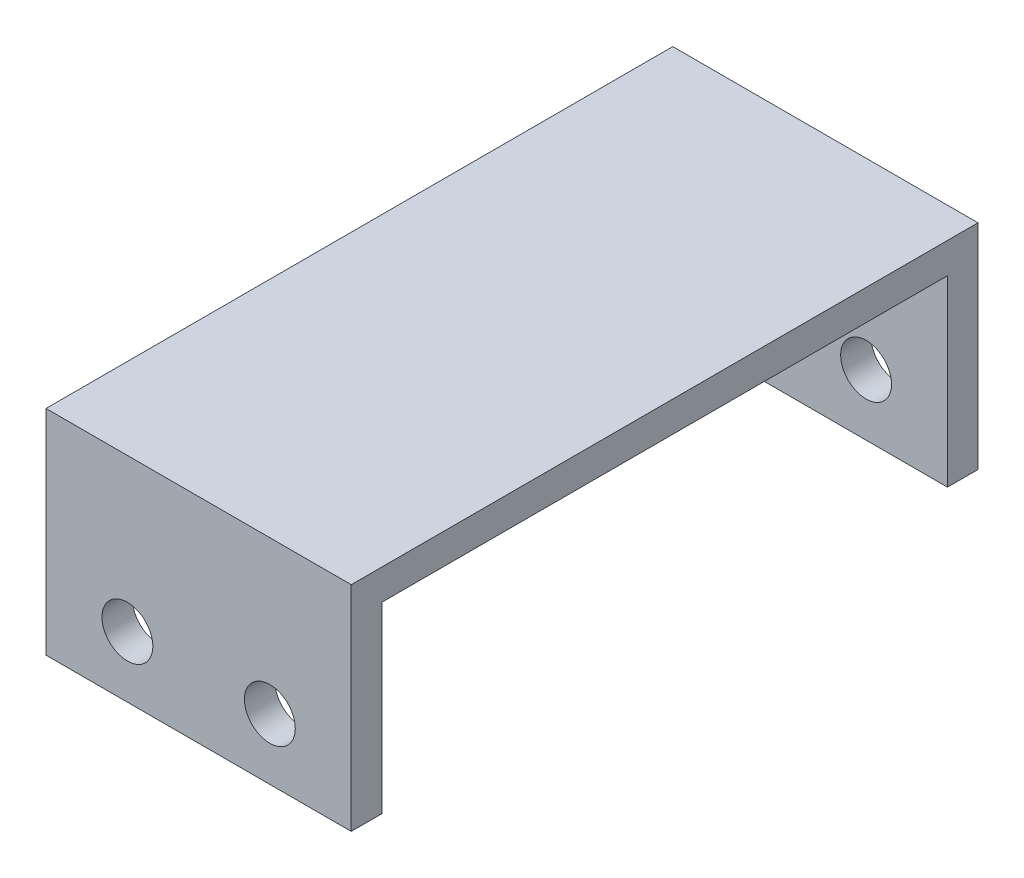
SolidWorks part; units mm, degrees
ref_plane "Front" through (0, 0, 0) normal (0, 0, 1) x (1, 0, 0)
ref_plane "Top" through (0, 0, 0) normal (0, 1, 0) x (1, 0, 0)
ref_plane "Right" through (0, 0, 0) normal (1, 0, 0) x (0, 0, -1)
sketch "草图1" plane through (0, 0, 0) normal (0, 1, 0) x (1, 0, 0)
  line L1 (-13.0818, 17.3503) -> (1.9182, 17.3503)
  line L2 (-13.0818, 17.3503) -> (-13.0818, -13.4497)
  line L3 (-13.0818, -13.4497) -> (1.9182, -13.4497)
  line L4 (1.9182, 17.3503) -> (1.9182, -13.4497)
  dimension "D1" = 30.8
  dimension "D2" = 15
extrude "凸台-拉伸1" add sketch "草图1" along normal blind 1.5
sketch "草图2" plane through (0, 0, 0) normal (0, -1, 0) x (1, 0, 0)
  line L0 (1.9182, 13.4497) -> (1.9182, -17.3503) construction
  line L1 (-13.0818, 13.4497) -> (1.9182, 13.4497)
  line L2 (-13.0818, 13.4497) -> (-13.0818, 11.9497)
  line L3 (-13.0818, 11.9497) -> (1.9182, 11.9497)
  line L4 (1.9182, 13.4497) -> (1.9182, 11.9497)
  line L6 (-13.0818, -17.3503) -> (1.9182, -17.3503)
  line L7 (-13.0818, -17.3503) -> (-13.0818, -15.8503)
  line L8 (-13.0818, -15.8503) -> (1.9182, -15.8503)
  line L9 (1.9182, -17.3503) -> (1.9182, -15.8503)
  dimension "D1" = 1.5
  dimension "D2" = 1.5
extrude "凸台-拉伸2" add sketch "草图2" along normal blind 9
sketch "草图3" plane through (0, 0, 13.4497) normal (0, 0, 1) x (1, 0, 0)
  line L1 (1.9182, -9) -> (-13.0818, -9) construction
  line L2 (-13.0818, 1.5) -> (-13.0818, -9) construction
  line L3 (1.9182, 1.5) -> (1.9182, -9) construction
  circle A0 centre (-9.0818, -6) radius 1.25
  circle A1 centre (-2.0818, -6) radius 1.25
  dimension "D1" = 2.5
  dimension "D2" = 2.5
  dimension "D3" = 3
  dimension "D4" = 3
  dimension "D5" = 4
  dimension "D6" = 4
extrude "切除-拉伸1" cut sketch "草图3" against normal through all both and the other way through all
